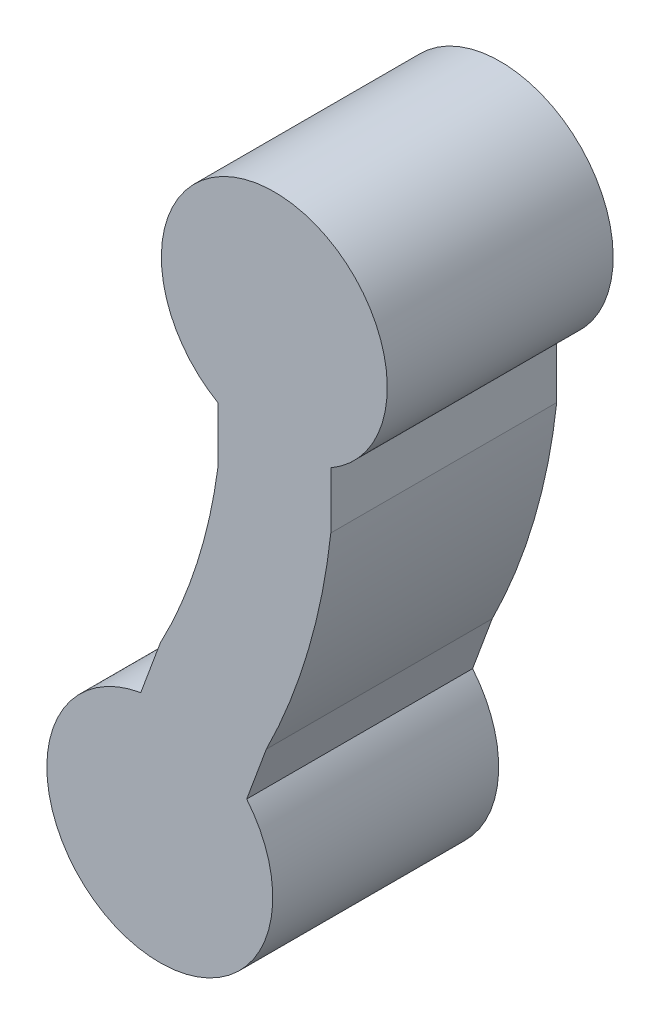
SolidWorks part; units mm, degrees
ref_plane "前视基准面" through (0, 0, 0) normal (0, 0, 1) x (1, 0, 0)
ref_plane "上视基准面" through (0, 0, 0) normal (0, 1, 0) x (1, 0, 0)
ref_plane "右视基准面" through (0, 0, 0) normal (1, 0, 0) x (0, 0, -1)
sketch "草图1" plane through (0, 0, 0) normal (0, 0, 1) x (1, 0, 0)
  line L0 (0.5, -1.366) -> (0.5, -0.866) construction
  line L1 (-0.5, -1.366) -> (-0.5, -0.866) construction
  line L2 (-0.2445, -3.7781) -> (-0.0711, -3.3092) construction
  line L3 (-1.1824, -3.4312) -> (-1.009, -2.9623) construction
  line L4 (0.5, -1.366) -> (0.5, -0.866)
  line L5 (-0.5, -1.366) -> (-0.5, -0.866)
  line L6 (-0.2445, -3.7781) -> (-0.0711, -3.3092)
  line L7 (-1.1824, -3.4312) -> (-1.009, -2.9623)
  line L8 (-0.5, -1.366) -> (0.5, -1.366) construction
  line L9 (-1.009, -2.9623) -> (-0.0711, -3.3092) construction
  line L10 (0, -1.366) -> (-0.54, -3.1357) construction
  line L11 (-0.27, -2.2509) -> (-4.0028, -1.1119) construction
  arc A0 (0.5, -0.866) -> (-0.5, -0.866) centre (0, 0) ccw construction
  arc A1 (0.5, -0.866) -> (-0.5, -0.866) centre (0, 0) ccw
  arc A2 (-1.1824, -3.4312) -> (-0.2445, -3.7781) centre (-1.0139, -4.4169) ccw construction
  arc A3 (-1.1824, -3.4312) -> (-0.2445, -3.7781) centre (-1.0139, -4.4169) ccw
  arc A4 (-1.009, -2.9623) -> (-0.5, -1.366) centre (-5.213, -0.7426) ccw
  arc A5 (-0.0711, -3.3092) -> (0.5, -1.366) centre (-5.213, -0.7426) ccw
extrude "凸台-拉伸1" add sketch "草图1" against normal blind 2
